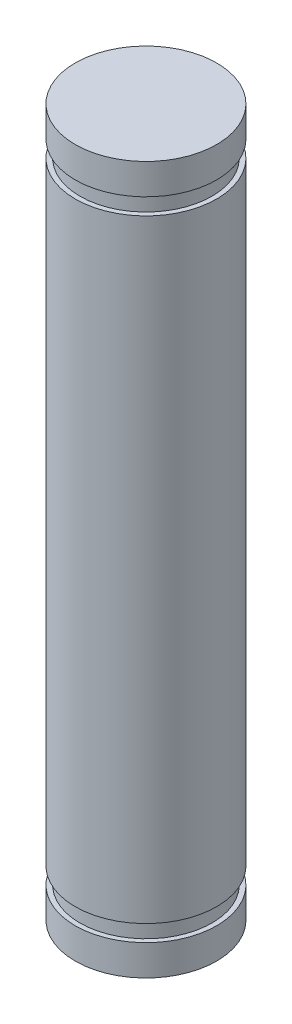
SolidWorks part; units mm, degrees
ref_plane "前视基准面" through (0, 0, 0) normal (0, 0, 1) x (1, 0, 0)
ref_plane "上视基准面" through (0, 0, 0) normal (0, 1, 0) x (1, 0, 0)
ref_plane "右视基准面" through (0, 0, 0) normal (1, 0, 0) x (0, 0, -1)
sketch "草图1" plane through (0, 0, 0) normal (0, 0, 1) x (1, 0, 0)
  line L0 (0, -15) -> (3, -15)
  line L1 (3, -15) -> (3, -13.7)
  line L2 (3, -13.7) -> (2.8, -13.7)
  line L3 (2.8, -13.7) -> (2.8, -13)
  line L4 (2.8, -13) -> (3, -13)
  line L5 (3, -13) -> (3, 13)
  line L6 (3, 13) -> (2.8, 13)
  line L7 (2.8, 13.7) -> (3, 13.7)
  line L8 (2.8, 13) -> (2.8, 13.7)
  line L9 (3, 13.7) -> (3, 15)
  line L10 (3, 15) -> (0, 15)
  line L11 (0, 15) -> (0, -15)
  dimension "D1" = 3
  dimension "D2" = 0.2
  dimension "D3" = 30
  dimension "D4" = 0.7
  dimension "D5" = 1.3
revolve "旋转1" add sketch "草图1" angle 360 about L11
